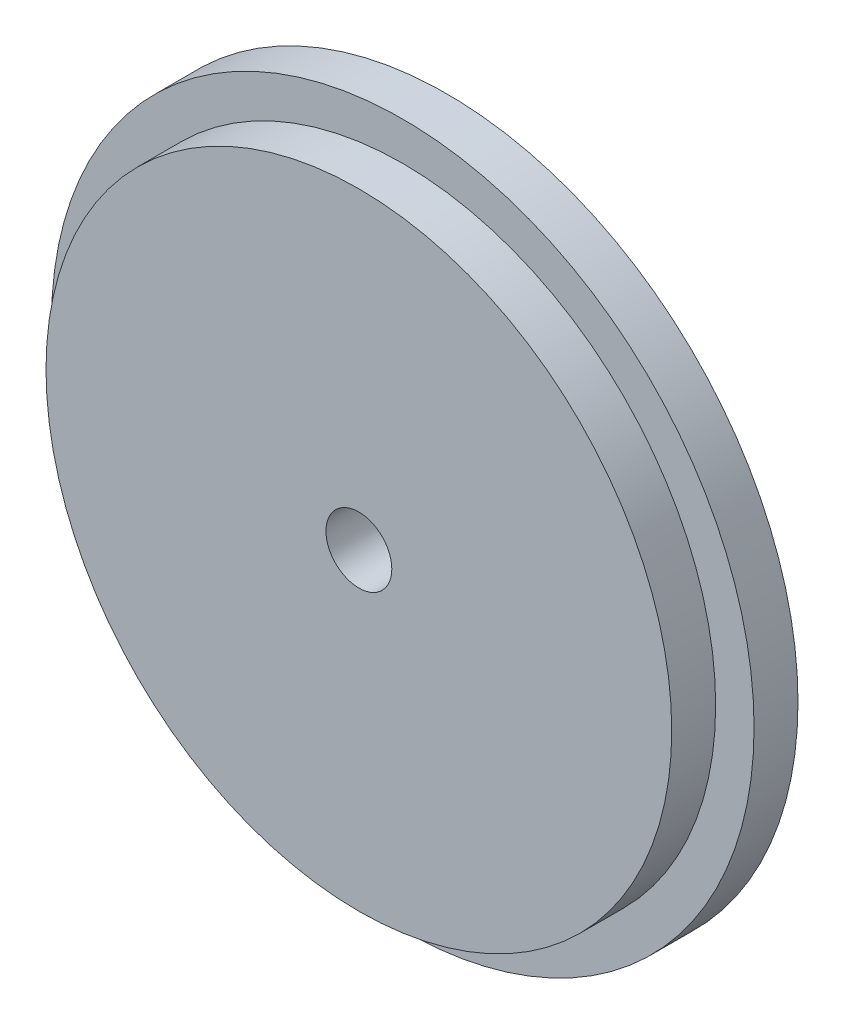
SolidWorks part; units mm, degrees
ref_plane "Plan de face" through (0, 0, 0) normal (0, 0, 1) x (1, 0, 0)
ref_plane "Plan de dessus" through (0, 0, 0) normal (0, 1, 0) x (1, 0, 0)
ref_plane "Plan de droite" through (0, 0, 0) normal (1, 0, 0) x (0, 0, -1)
sketch "Esquisse1" plane through (0, 0, 0) normal (0, 0, 1) x (1, 0, 0)
  circle A0 centre (0, 0) radius 16
  dimension "D1" = 32
extrude "Boss.-Extru.1" add sketch "Esquisse1" along normal blind 2
sketch "Esquisse2" plane through (0, 0, 2) normal (0, 0, 1) x (1, 0, 0)
  circle A0 centre (0, 0) radius 14.25
  dimension "D1" = 28.5
extrude "Boss.-Extru.2" add sketch "Esquisse2" along normal blind 2
sketch "Esquisse3" plane through (0, 0, 4) normal (0, 0, 1) x (1, 0, 0)
  circle A0 centre (0, 0) radius 1.5
  dimension "D1" = 3
extrude "Enlèv. mat.-Extru.1" cut sketch "Esquisse3" against normal through all
